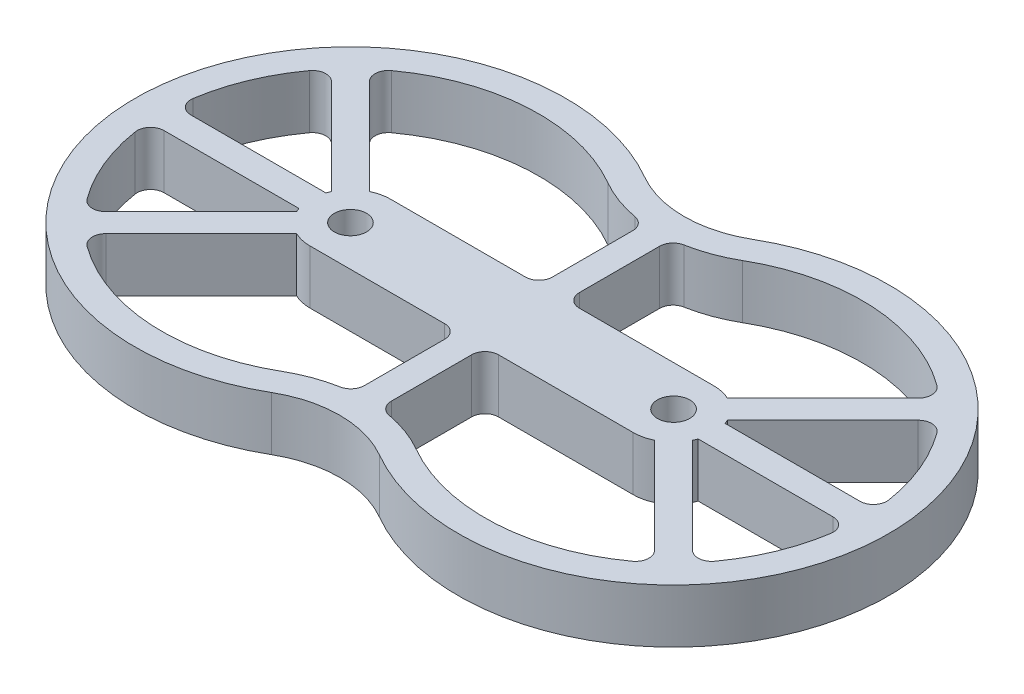
SolidWorks part; units mm, degrees
ref_plane "Front Plane" through (0, 0, 0) normal (0, 0, 1) x (1, 0, 0)
ref_plane "Top Plane" through (0, 0, 0) normal (0, 1, 0) x (1, 0, 0)
ref_plane "Right Plane" through (0, 0, 0) normal (1, 0, 0) x (0, 0, -1)
sketch "Sketch1" plane through (0, 0, 0) normal (0, 1, 0) x (1, 0, 0)
  line L0 (55, 20) -> (55, 49.8398)
  line L1 (0, 15) -> (50, 15)
  line L2 (0, -15) -> (50, -15)
  line L3 (65, 20) -> (65, 49.8398)
  line L4 (0, 0) -> (6, 0)
  line L5 (55, -20) -> (55, -49.8398)
  line L6 (65, -20) -> (65, -49.8398)
  line L7 (70, 15) -> (120, 15)
  line L8 (70, -15) -> (120, -15)
  line L9 (134.1421, 5) -> (184.2262, 5)
  line L10 (134.1421, -5) -> (184.2262, -5)
  line L11 (-6.4645, 13.5355) -> (-41.8792, 48.9503)
  line L12 (-6.4645, -13.5355) -> (-41.8792, -48.9503)
  line L13 (120, 0) -> (176.5685, -56.5685) construction
  line L14 (126.4645, -13.5355) -> (161.8792, -48.9503)
  line L15 (-13.5355, 6.4645) -> (-48.9503, 41.8792)
  line L16 (-14.1421, 5) -> (-64.2262, 5)
  line L17 (-14.1421, -5) -> (-64.2262, -5)
  line L18 (133.5355, -6.4645) -> (168.9503, -41.8792)
  line L19 (-13.5355, -6.4645) -> (-48.9503, -41.8792)
  line L20 (0, 0) -> (-56.5685, -56.5685) construction
  line L21 (120, 0) -> (169.371, 49.371) construction
  line L22 (120, 0) -> (213.4915, 0) construction
  line L23 (0, 0) -> (120, 0) construction
  line L24 (0, 0) -> (-101.0897, 0) construction
  line L25 (0, 0) -> (-61.8661, 61.8661) construction
  line L26 (126.4645, 13.5355) -> (161.8792, 48.9503)
  line L27 (133.5355, 6.4645) -> (168.9503, 41.8792)
  line L29 (60, 55.9552) -> (60, -56.5232) construction
  arc A0 (40, 69.282) -> (40, -69.282) centre (0, 0) ccw
  arc A5 (80, -69.282) -> (80, 69.282) centre (120, 0) ccw
  circle A6 centre (0, 0) radius 6
  circle A7 centre (120, 0) radius 6
  arc A9 (80, 69.282) -> (40, 69.282) centre (60, 103.923) cw
  arc A10 (80, -69.282) -> (40, -69.282) centre (60, -103.923) ccw
  arc A12 (85, 60.6218) -> (69.0909, 54.7564) centre (60, 103.923) cw
  arc A15 (85, -60.6218) -> (161.2932, -56.5232) centre (120, 0) ccw
  arc A16 (35, 60.6218) -> (-41.2932, 56.5232) centre (0, 0) ccw
  arc A17 (85, -60.6218) -> (69.0909, -54.7564) centre (60, -103.923) ccw
  arc A18 (50.9091, -54.7564) -> (35, -60.6218) centre (60, -103.923) ccw
  arc A19 (85, -60.6218) -> (35, -60.6218) centre (60, -103.923) ccw construction
  arc A20 (50.9091, 54.7564) -> (35, 60.6218) centre (60, 103.923) cw
  arc A21 (85, 60.6218) -> (35, 60.6218) centre (60, 103.923) cw construction
  arc A22 (55, 49.8398) -> (50.9091, 54.7564) centre (50, 49.8398) ccw
  arc A23 (65, 49.8398) -> (69.0909, 54.7564) centre (70, 49.8398) cw
  arc A24 (55, -49.8398) -> (50.9091, -54.7564) centre (50, -49.8398) cw
  arc A25 (65, -49.8398) -> (69.0909, -54.7564) centre (70, -49.8398) ccw
  arc A26 (55, -20) -> (50, -15) centre (50, -20) ccw
  arc A27 (65, -20) -> (70, -15) centre (70, -20) cw
  arc A28 (55, 20) -> (50, 15) centre (50, 20) cw
  arc A29 (65, 20) -> (70, 15) centre (70, 20) ccw
  arc A30 (-69.1666, -10.7692) -> (-56.5232, -41.2932) centre (0, 0) ccw
  arc A31 (35, 60.6218) -> (35, -60.6218) centre (0, 0) ccw construction
  arc A32 (189.1666, 10.7692) -> (176.5232, 41.2932) centre (120, 0) ccw
  arc A33 (85, -60.6218) -> (85, 60.6218) centre (120, 0) ccw construction
  arc A34 (-41.2932, -56.5232) -> (35, -60.6218) centre (0, 0) ccw
  arc A35 (-56.5232, 41.2932) -> (-69.1666, 10.7692) centre (0, 0) ccw
  arc A36 (176.5232, -41.2932) -> (189.1666, -10.7692) centre (120, 0) ccw
  arc A37 (161.2932, 56.5232) -> (85, 60.6218) centre (120, 0) ccw
  arc A38 (-48.9503, 41.8792) -> (-56.5232, 41.2932) centre (-52.4858, 38.3437) ccw
  arc A39 (-64.2262, 5) -> (-69.1666, 10.7692) centre (-64.2262, 10) cw
  arc A40 (-64.2262, -5) -> (-69.1666, -10.7692) centre (-64.2262, -10) ccw
  arc A41 (-48.9503, -41.8792) -> (-56.5232, -41.2932) centre (-52.4858, -38.3437) cw
  arc A42 (-41.8792, 48.9503) -> (-41.2932, 56.5232) centre (-38.3437, 52.4858) cw
  arc A43 (-41.8792, -48.9503) -> (-41.2932, -56.5232) centre (-38.3437, -52.4858) ccw
  arc A44 (161.8792, -48.9503) -> (161.2932, -56.5232) centre (158.3437, -52.4858) cw
  arc A45 (168.9503, -41.8792) -> (176.5232, -41.2932) centre (172.4858, -38.3437) ccw
  arc A46 (184.2262, -5) -> (189.1666, -10.7692) centre (184.2262, -10) cw
  arc A47 (168.9503, 41.8792) -> (176.5232, 41.2932) centre (172.4858, 38.3437) cw
  arc A48 (184.2262, 5) -> (189.1666, 10.7692) centre (184.2262, 10) ccw
  arc A49 (161.8792, 48.9503) -> (161.2932, 56.5232) centre (158.3437, 52.4858) ccw
  arc A56 (-14.1421, -5) -> (-13.5355, -6.4645) centre (0, 0) ccw
  arc A59 (120, -15) -> (126.4645, -13.5355) centre (120, 0) ccw
  circle A60 centre (0, 0) radius 15 construction
  arc A61 (-13.5355, 6.4645) -> (-14.1421, 5) centre (0, 0) ccw
  arc A63 (0, 15) -> (-6.4645, 13.5355) centre (0, 0) ccw
  arc A64 (-6.4645, -13.5355) -> (0, -15) centre (0, 0) ccw
  circle A65 centre (120, 0) radius 15 construction
  arc A66 (133.5355, -6.4645) -> (134.1421, -5) centre (120, 0) ccw
  arc A67 (134.1421, 5) -> (133.5355, 6.4645) centre (120, 0) ccw
  arc A68 (126.4645, 13.5355) -> (120, 15) centre (120, 0) ccw
  point P38 (55, 54.1737)
  point P43 (55, -54.1737)
  point P51 (65, -15)
  point P54 (55, 15)
  point P57 (65, 15)
  point P81 (-52.9066, 45.8355)
  point P84 (-69.8212, 5)
  point P87 (-69.8212, -5)
  point P90 (-52.9066, -45.8355)
  point P93 (-45.8355, 52.9066)
  point P96 (-45.8355, -52.9066)
  point P99 (165.8355, -52.9066)
  point P102 (172.9066, -45.8355)
  point P107 (172.9066, 45.8355)
  point P110 (189.8212, 5)
  point P113 (165.8355, 52.9066)
  point P116 (127.9289, 15)
  point P119 (127.9289, -15)
  point P122 (-7.9289, 15)
  point P125 (-7.9289, -15)
  point P126 (127.2086, 14.2796)
  point P128 (127.2086, -14.2841)
  point P129 (-7.2116, -14.2826)
  point P131 (-7.9289, 15)
  point P133 (126.5504, 13.6215)
  dimension "D2" = 10
  dimension "D3" = 10
  dimension "D4" = 12
  dimension "D5" = 45
  dimension "D7" = 10
  dimension "D8" = 120
  dimension "D10" = 80
  dimension "D11" = 80
  dimension "D12" = 40
  dimension "D13" = 40
  dimension "D14" = 10
  dimension "D17" = 5
  dimension "D18" = 5
  dimension "D20" = 5
  dimension "D21" = 5
  dimension "D22" = 5
  dimension "D23" = 5
  dimension "D24" = 5
  dimension "D25" = 5
  dimension "D45" = 5
  dimension "D46" = 5
  dimension "D47" = 5
  dimension "D48" = 5
  dimension "D49" = 5
  dimension "D50" = 5
  dimension "D51" = 5
  dimension "D52" = 5
  dimension "D53" = 5
  dimension "D54" = 5
  dimension "D55" = 5
  dimension "D56" = 5
  dimension "D57" = 9
  dimension "D59" = 9
  dimension "D60" = 5
  dimension "D64" = 12
  dimension "D9" = 30
  dimension "D15" = 5
  dimension "D16" = 5
  dimension "D19" = 10
  dimension "D26" = 5
  dimension "D27" = 5
  dimension "D28" = 5
  dimension "D29" = 45
  dimension "D30" = 5
  dimension "D31" = 5
  dimension "D32" = 10
  dimension "D33" = 5
  dimension "D34" = 45
  dimension "D35" = 5
  dimension "D36" = 5
  dimension "D37" = 5
  dimension "D38" = 10
  dimension "D39" = 5
  dimension "D40" = 5
  dimension "D41" = 5
  dimension "D42" = 5
  dimension "D43" = 5
  dimension "D44" = 5
  dimension "D62" = 15
  dimension "D63" = 5
  dimension "D65" = 45
  dimension "D66" = 5
extrude "Boss-Extrude1" add sketch "Sketch1" along normal blind 20
